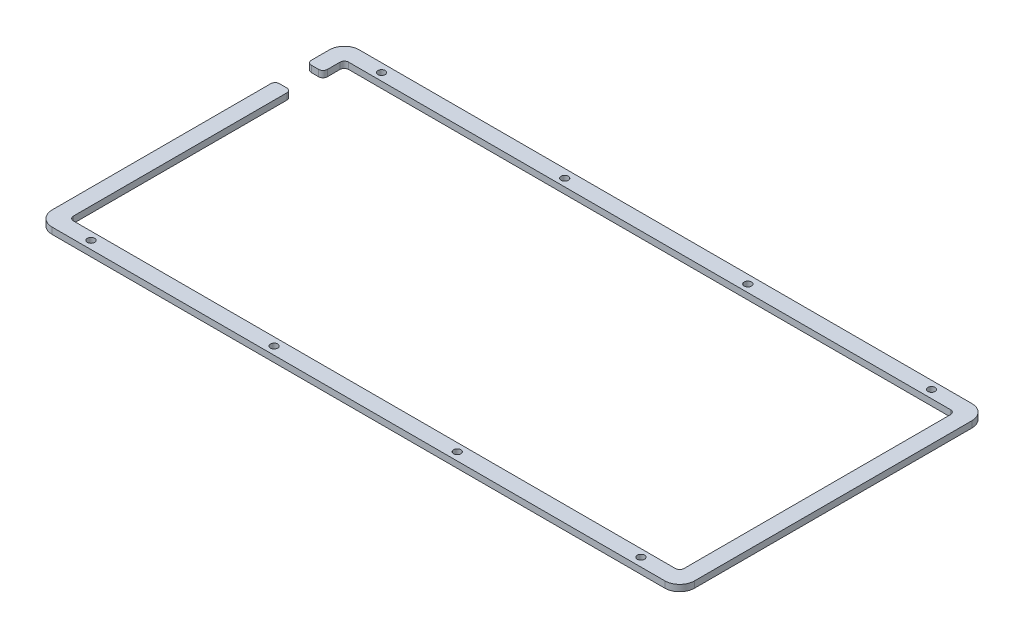
SolidWorks part; units mm, degrees
ref_plane "Front Plane" through (0, 0, 0) normal (0, 0, 1) x (1, 0, 0)
ref_plane "Top Plane" through (0, 0, 0) normal (0, 1, 0) x (1, 0, 0)
ref_plane "Right Plane" through (0, 0, 0) normal (1, 0, 0) x (0, 0, -1)
sketch "Sketch1" plane through (0, 0, 0) normal (0, 1, 0) x (1, 0, 0)
  line L1 (0, 0) -> (350, 0)
  line L2 (0, 0) -> (0, 200)
  line L3 (0, 200) -> (350, 200)
  line L4 (350, 0) -> (350, 200)
extrude "Boss-Extrude1" add sketch "Sketch1" along normal blind 3
sketch "Sketch2" plane through (0, 3, 0) normal (0, 1, 0) x (1, 0, 0)
  line L0 (334.4538, 22.4974) -> (46.7545, 22.4974)
  line L1 (341.4538, 159.6969) -> (341.4538, 29.4974)
  line L2 (46.7545, 166.6969) -> (334.4538, 166.6969)
  line L3 (333.9538, 31.9974) -> (333.9538, 157.1969)
  line L4 (331.9538, 29.9974) -> (49.2545, 29.9974)
  line L5 (39.7545, 132.1969) -> (39.7545, 29.4974)
  line L6 (45.2545, 134.1969) -> (41.7545, 134.1969)
  line L7 (47.2545, 132.1969) -> (47.2545, 31.9974)
  line L8 (41.7545, 149.1969) -> (45.2545, 149.1969)
  line L9 (39.7545, 151.1969) -> (39.7545, 159.6969)
  line L10 (47.2545, 157.1969) -> (47.2545, 151.1969)
  line L11 (49.2545, 159.1969) -> (331.9538, 159.1969)
  circle A0 centre (319.2545, 26.4974) radius 1.7
  circle A1 centre (233.2545, 26.2474) radius 1.7
  circle A2 centre (61.2545, 26.2474) radius 1.7
  circle A3 centre (147.2545, 26.2474) radius 1.7
  circle A4 centre (319.2545, 162.9469) radius 1.7
  circle A5 centre (233.2545, 162.6969) radius 1.7
  circle A6 centre (61.2545, 162.6969) radius 1.7
  circle A7 centre (147.2545, 162.6969) radius 1.7
  arc A8 (46.7545, 166.6969) -> (39.7545, 159.6969) centre (46.7545, 159.6969) ccw
  arc A9 (39.7545, 29.4974) -> (46.7545, 22.4974) centre (46.7545, 29.4974) ccw
  arc A10 (334.4538, 22.4974) -> (341.4538, 29.4974) centre (334.4538, 29.4974) ccw
  arc A11 (341.4538, 159.6969) -> (334.4538, 166.6969) centre (334.4538, 159.6969) ccw
  arc A12 (333.9538, 157.1969) -> (331.9538, 159.1969) centre (331.9538, 157.1969) ccw
  arc A13 (331.9538, 29.9974) -> (333.9538, 31.9974) centre (331.9538, 31.9974) ccw
  arc A14 (47.2545, 31.9974) -> (49.2545, 29.9974) centre (49.2545, 31.9974) ccw
  arc A15 (41.7545, 134.1969) -> (39.7545, 132.1969) centre (41.7545, 132.1969) ccw
  arc A16 (47.2545, 132.1969) -> (45.2545, 134.1969) centre (45.2545, 132.1969) ccw
  arc A17 (45.2545, 149.1969) -> (47.2545, 151.1969) centre (45.2545, 151.1969) ccw
  arc A18 (39.7545, 151.1969) -> (41.7545, 149.1969) centre (41.7545, 151.1969) ccw
  arc A19 (49.2545, 159.1969) -> (47.2545, 157.1969) centre (49.2545, 157.1969) ccw
extrude "Cut-Extrude1" cut sketch "Sketch2" against normal blind 10 flip side to cut
